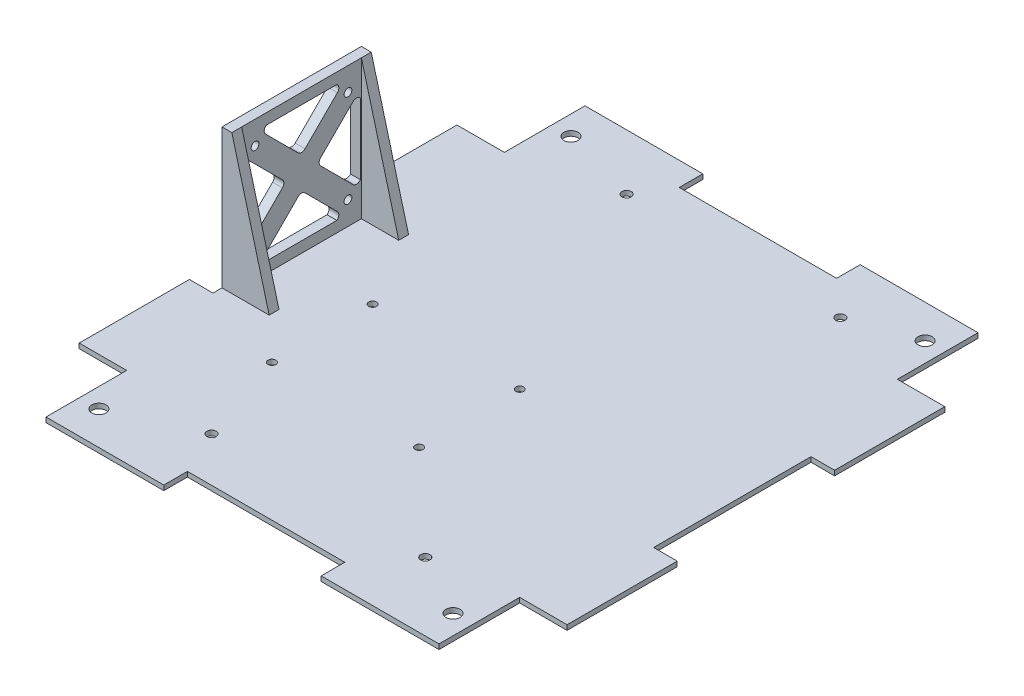
SolidWorks part; units mm, degrees
ref_plane "Front Plane" through (0, 0, 0) normal (0, 0, 1) x (1, 0, 0)
ref_plane "Top Plane" through (0, 0, 0) normal (0, 1, 0) x (1, 0, 0)
ref_plane "Right Plane" through (0, 0, 0) normal (1, 0, 0) x (0, 0, -1)
sketch "Sketch1" plane through (0, 0, 0) normal (0, 1, 0) x (1, 0, 0)
  line L0 (-25.4, 86.995) -> (-63.4314, 86.995)
  line L1 (-88.9, -101.6) -> (88.9, -101.6) construction
  line L2 (101.6, -88.9) -> (101.6, 88.9) construction
  line L3 (88.9, 101.6) -> (-88.9, 101.6) construction
  line L4 (-78.74, -60.96) -> (-63.4314, -60.96)
  line L5 (-63.4314, -60.96) -> (-63.4314, -86.995)
  line L6 (-63.4314, -86.995) -> (-25.4, -86.995)
  line L7 (63.4314, -86.995) -> (63.4314, -60.96)
  line L8 (63.4314, -60.96) -> (78.74, -60.96)
  line L9 (78.74, -60.96) -> (78.74, -25.4)
  line L10 (78.74, 60.96) -> (63.4314, 60.96)
  line L11 (63.4314, 60.96) -> (63.4314, 86.995)
  line L12 (63.4314, 86.995) -> (25.4, 86.995)
  line L13 (-63.4314, 86.995) -> (-63.4314, 60.96)
  line L14 (-63.4314, 60.96) -> (-78.74, 60.96)
  line L15 (-78.74, 60.96) -> (-78.74, 25.4)
  line L16 (-78.74, -25.4) -> (-78.74, -60.96)
  line L17 (-78.74, -25.4) -> (-71.12, -25.4)
  line L19 (-78.74, 25.4) -> (-71.12, 25.4)
  line L20 (-71.12, -25.4) -> (-71.12, 25.4)
  line L22 (-25.4, 86.995) -> (-25.4, 79.375)
  line L23 (-25.4, 79.375) -> (25.4, 79.375)
  line L24 (25.4, 86.995) -> (25.4, 79.375)
  line L25 (78.74, 25.4) -> (71.12, 25.4)
  line L27 (78.74, -25.4) -> (71.12, -25.4)
  line L28 (71.12, 25.4) -> (71.12, -25.4)
  line L30 (25.4, -86.995) -> (25.4, -79.375)
  line L31 (25.4, -79.375) -> (-25.4, -79.375)
  line L32 (-25.4, -86.995) -> (-25.4, -79.375)
  line L33 (78.74, 25.4) -> (78.74, 60.96)
  line L34 (25.4, -86.995) -> (63.4314, -86.995)
  line L35 (-101.6, 88.9) -> (-101.6, -88.9) construction
  arc A0 (88.9, -101.6) -> (101.6, -88.9) centre (88.9, -88.9) ccw construction
  arc A1 (-101.6, -88.9) -> (-88.9, -101.6) centre (-88.9, -88.9) ccw construction
  arc A2 (101.6, 88.9) -> (88.9, 101.6) centre (88.9, 88.9) ccw construction
  arc A3 (-101.6, 88.9) -> (-88.9, 101.6) centre (-88.9, 88.9) cw construction
  circle A4 centre (-57.15, 76.2) radius 2.286
  circle A5 centre (57.15, 76.2) radius 2.286
  circle A6 centre (57.15, -76.2) radius 2.286
  circle A7 centre (-57.15, -76.2) radius 2.286
  point P3 (0, 101.6)
  point P5 (101.6, 0)
  point P13 (101.6, 101.6)
  point P16 (-101.6, 101.6)
  point P38 (-71.12, 0)
  point P55 (0, -79.375)
  point P56 (0, 79.375)
  point P57 (71.12, 0)
  dimension "D2" = 12.7
  dimension "D11" = 4.572
  dimension "D8" = 44.45
  dimension "D1" = 203.2
  dimension "D3" = 203.2
  dimension "D4" = 22.86
  dimension "D5" = 15.3086
  dimension "D6" = 35.56
  dimension "D7" = 173.99
  dimension "D12" = 50.8
  dimension "D13" = 25.4
  dimension "D14" = 44.45
  dimension "D15" = 25.4
  dimension "D18" = 7.62
extrude "Main Body" add sketch "Sketch1" along normal blind 1.5875
sketch "Sketch8" plane through (0, 1.5875, 0) normal (0, 1, 0) x (1, 0, 0)
  line L1 (-71.12, 22.5) -> (-67.945, 22.5)
  line L2 (-71.12, 22.5) -> (-71.12, -22.5)
  line L3 (-71.12, -22.5) -> (-67.945, -22.5)
  line L4 (-67.945, 22.5) -> (-67.945, -22.5)
  line L5 (-71.12, 22.5) -> (-67.945, -22.5) construction
  line L6 (-71.12, -22.5) -> (-67.945, 22.5) construction
  line L34 (71.12, -25.4) -> (71.12, 25.4)
  line L35 (71.12, 25.4) -> (78.74, 25.4)
  line L36 (78.74, 25.4) -> (78.74, 60.96)
  line L37 (78.74, 60.96) -> (63.4314, 60.96)
  line L38 (63.4314, 60.96) -> (63.4314, 86.995)
  line L39 (63.4314, 86.995) -> (25.4, 86.995)
  line L40 (25.4, 86.995) -> (25.4, 79.375)
  line L41 (25.4, 79.375) -> (-25.4, 79.375)
  line L42 (-25.4, 79.375) -> (-25.4, 86.995)
  line L43 (-25.4, 86.995) -> (-63.4314, 86.995)
  line L44 (-63.4314, 86.995) -> (-63.4314, 60.96)
  line L45 (-63.4314, 60.96) -> (-78.74, 60.96)
  line L46 (-78.74, 60.96) -> (-78.74, 25.4)
  line L47 (-78.74, 25.4) -> (-71.12, 25.4)
  line L48 (-71.12, 25.4) -> (-71.12, -25.4)
  line L49 (-71.12, -25.4) -> (-78.74, -25.4)
  line L50 (-78.74, -25.4) -> (-78.74, -60.96)
  line L51 (-78.74, -60.96) -> (-63.4314, -60.96)
  line L52 (-63.4314, -60.96) -> (-63.4314, -86.995)
  line L53 (-63.4314, -86.995) -> (-25.4, -86.995)
  line L54 (-25.4, -86.995) -> (-25.4, -79.375)
  line L55 (-25.4, -79.375) -> (25.4, -79.375)
  line L56 (25.4, -79.375) -> (25.4, -86.995)
  line L57 (25.4, -86.995) -> (63.4314, -86.995)
  line L58 (63.4314, -86.995) -> (63.4314, -60.96)
  line L59 (63.4314, -60.96) -> (78.74, -60.96)
  line L60 (78.74, -60.96) -> (78.74, -25.4)
  line L61 (78.74, -25.4) -> (71.12, -25.4)
  line L66 (71.12, -25.4) -> (71.12, 25.4)
  line L67 (71.12, 25.4) -> (78.74, 25.4)
  line L68 (78.74, 25.4) -> (78.74, 60.96)
  line L69 (78.74, 60.96) -> (63.4314, 60.96)
  line L70 (63.4314, 60.96) -> (63.4314, 86.995)
  line L71 (63.4314, 86.995) -> (25.4, 86.995)
  line L72 (25.4, 86.995) -> (25.4, 79.375)
  line L73 (25.4, 79.375) -> (-25.4, 79.375)
  line L74 (-25.4, 79.375) -> (-25.4, 86.995)
  line L75 (-25.4, 86.995) -> (-63.4314, 86.995)
  line L76 (-63.4314, 86.995) -> (-63.4314, 60.96)
  line L77 (-63.4314, 60.96) -> (-78.74, 60.96)
  line L78 (-78.74, 60.96) -> (-78.74, 25.4)
  line L79 (-78.74, 25.4) -> (-71.12, 25.4)
  line L80 (-71.12, 25.4) -> (-71.12, -25.4)
  line L81 (-71.12, -25.4) -> (-78.74, -25.4)
  line L82 (-78.74, -25.4) -> (-78.74, -60.96)
  line L83 (-78.74, -60.96) -> (-63.4314, -60.96)
  line L84 (-63.4314, -60.96) -> (-63.4314, -86.995)
  line L85 (-63.4314, -86.995) -> (-25.4, -86.995)
  line L86 (-25.4, -86.995) -> (-25.4, -79.375)
  line L87 (-25.4, -79.375) -> (25.4, -79.375)
  line L88 (25.4, -79.375) -> (25.4, -86.995)
  line L89 (25.4, -86.995) -> (63.4314, -86.995)
  line L90 (63.4314, -86.995) -> (63.4314, -60.96)
  line L91 (63.4314, -60.96) -> (78.74, -60.96)
  line L92 (78.74, -60.96) -> (78.74, -25.4)
  line L93 (78.74, -25.4) -> (71.12, -25.4)
  point P2 (-71.12, 0)
  point P4 (-69.5325, 0)
  line M61 (-71.12, 25.4) -> (-71.12, -25.4)
  dimension "D2" = 3.175
  dimension "D3" = 45
  dimension "D1" = 0
extrude "Boss-Extrude4" add sketch "Sketch8" along normal blind 45 contours L4 L1 L3 M61
sketch "Sketch9" plane through (-71.12, 0, 0) normal (-1, 0, 0) x (0, 0, 1)
  line L2 (-19, 5.0875) -> (19, 5.0875)
  line L3 (-19, 5.0875) -> (-19, 43.0875)
  line L4 (-19, 43.0875) -> (19, 43.0875)
  line L5 (19, 5.0875) -> (19, 43.0875)
  line L8 (-25.4, 0) -> (25.4, 0)
  line L9 (25.4, 0) -> (25.4, 1.5875)
  line L10 (25.4, 1.5875) -> (22.5, 1.5875)
  line L11 (22.5, 1.5875) -> (22.5, 46.5875)
  line L12 (22.5, 46.5875) -> (-22.5, 46.5875)
  line L13 (-22.5, 46.5875) -> (-22.5, 1.5875)
  line L14 (-22.5, 1.5875) -> (-25.4, 1.5875)
  line L15 (-25.4, 1.5875) -> (-25.4, 0)
  line L16 (-25.4, 0) -> (25.4, 0)
  line L17 (25.4, 0) -> (25.4, 1.5875)
  line L18 (25.4, 1.5875) -> (22.5, 1.5875)
  line L19 (22.5, 1.5875) -> (22.5, 46.5875)
  line L20 (22.5, 46.5875) -> (-22.5, 46.5875)
  line L21 (-22.5, 46.5875) -> (-22.5, 1.5875)
  line L22 (-22.5, 1.5875) -> (-25.4, 1.5875)
  line L23 (-25.4, 1.5875) -> (-25.4, 0)
  line L24 (-1.1225, 30.2475) -> (-11.5775, 40.7025)
  line L25 (1.1225, 30.2475) -> (11.5775, 40.7025)
  line L26 (10.4549, 43.4125) -> (-10.4549, 43.4125)
  line L27 (19.325, 13.6326) -> (19.325, 34.5424)
  line L28 (6.16, 25.21) -> (16.615, 35.665)
  line L29 (6.16, 22.965) -> (16.615, 12.51)
  line L30 (-10.4549, 4.7625) -> (10.4549, 4.7625)
  line L31 (1.1225, 17.9275) -> (11.5775, 7.4725)
  line L32 (-1.1225, 17.9275) -> (-11.5775, 7.4725)
  line L33 (-19.325, 34.5424) -> (-19.325, 13.6326)
  line L34 (-6.16, 22.965) -> (-16.615, 12.51)
  line L35 (-6.16, 25.21) -> (-16.615, 35.665)
  circle A0 centre (-15, 39.0875) radius 1.25
  circle A1 centre (15, 39.0875) radius 1.25
  circle A2 centre (-15, 9.0875) radius 1.25
  circle A3 centre (15, 9.0875) radius 1.25
  arc A4 (10.4549, 43.4125) -> (11.5775, 40.7025) centre (10.4549, 41.825) cw
  arc A5 (1.1225, 30.2475) -> (-1.1225, 30.2475) centre (0, 31.3701) cw
  arc A6 (-11.5775, 40.7025) -> (-10.4549, 43.4125) centre (-10.4549, 41.825) cw
  arc A7 (16.615, 35.665) -> (19.325, 34.5424) centre (17.7375, 34.5424) cw
  arc A8 (19.325, 13.6326) -> (16.615, 12.51) centre (17.7375, 13.6326) cw
  arc A9 (6.16, 22.965) -> (6.16, 25.21) centre (7.2826, 24.0875) cw
  arc A10 (11.5775, 7.4725) -> (10.4549, 4.7625) centre (10.4549, 6.35) cw
  arc A11 (-10.4549, 4.7625) -> (-11.5775, 7.4725) centre (-10.4549, 6.35) cw
  arc A12 (-1.1225, 17.9275) -> (1.1225, 17.9275) centre (0, 16.8049) cw
  arc A13 (-16.615, 12.51) -> (-19.325, 13.6326) centre (-17.7375, 13.6326) cw
  arc A14 (-19.325, 34.5424) -> (-16.615, 35.665) centre (-17.7375, 34.5424) cw
  arc A15 (-6.16, 25.21) -> (-6.16, 22.965) centre (-7.2826, 24.0875) cw
  point P24 (0, 29.125)
  point P30 (14.2875, 43.4125)
  point P33 (0, 29.125)
  point P36 (-14.2875, 43.4125)
  point P67 (0, 24.0875)
  dimension "D6" = 2.5
  dimension "D15" = 1.5875
  dimension "D18" = 22.5
  dimension "D2" = 19
  dimension "D3" = 19
  dimension "D4" = 38
  dimension "D5" = 38
  dimension "D7" = 4
  dimension "D8" = 4
  dimension "D9" = 4
  dimension "D10" = 4
  dimension "D11" = 45
  dimension "D12" = 45
  dimension "D13" = 28.575
  dimension "D14" = 3.175
  dimension "D17" = 5.0375
  dimension "D19" = 22.5
  dimension "D1" = 0
  dimension "D16" = 4
sketch "Sketch10" plane through (0, 0, 22.5) normal (0, 0, 1) x (1, 0, 0)
  line L3 (-67.945, 46.5875) -> (-67.945, 1.5875) construction
  line L4 (-67.945, 46.5875) -> (-67.945, 1.5875)
  line L5 (-67.945, 46.5875) -> (-55.8873, 1.5875)
  line L6 (-55.8873, 1.5875) -> (-67.945, 1.5875)
  dimension "D1" = 15
extrude "Boss-Extrude5" add sketch "Sketch10" against normal blind 3.175 contours L6 L4 L5
mirror "Mirror3" about plane through (0, 0, 0) normal (0, 0, 1) of "Boss-Extrude5"
extrude "Cut-Extrude2" cut sketch "Sketch9" against normal up to next contours A15 L35 A14 L3 A13 L34 | A9 L29 A8 L5 A7 L28 | A12 L32 A11 L2 A10 L31 | A6 L24 A5 L25 A4 L4 | A1 | A0 | A2 | A3
sketch "Sketch12" plane through (0, 0, 0) normal (0, -1, 0) x (1, 0, 0)
  line L1 (-45, -80) -> (45, -80)
  line L2 (-45, -80) -> (-45, 80)
  line L3 (-45, 80) -> (45, 80)
  line L4 (45, -80) -> (45, 80)
  line L5 (-45, -80) -> (45, 80) construction
  line L6 (-45, 80) -> (45, -80) construction
  line L7 (-39.779, -55.547) -> (-27.7357, -55.547)
  line L8 (-39.779, -55.547) -> (-39.779, -29.6043)
  line L9 (-39.779, -29.6043) -> (-27.7357, -29.6043)
  line L10 (-27.7357, -55.547) -> (-27.7357, -29.6043)
  line L11 (-39.779, -55.547) -> (-27.7357, -29.6043) construction
  line L12 (-39.779, -29.6043) -> (-27.7357, -55.547) construction
  line L13 (-29.9932, -76.7863) -> (-5.1713, -76.7863)
  line L14 (-29.9932, -76.7863) -> (-29.9932, -67.2902)
  line L15 (-29.9932, -67.2902) -> (-5.1713, -67.2902)
  line L16 (-5.1713, -76.7863) -> (-5.1713, -67.2902)
  line L17 (-29.9932, -76.7863) -> (-5.1713, -67.2902) construction
  line L18 (-29.9932, -67.2902) -> (-5.1713, -76.7863) construction
  line L28 (-78.74, 60.96) -> (-78.74, 25.4)
  line L29 (-78.74, 25.4) -> (-71.12, 25.4)
  line L30 (-71.12, 25.4) -> (-71.12, -25.4)
  line L31 (-71.12, -25.4) -> (-78.74, -25.4)
  line L32 (-78.74, -25.4) -> (-78.74, -60.96)
  line L33 (-78.74, -60.96) -> (-63.4314, -60.96)
  line L34 (-63.4314, -60.96) -> (-63.4314, -86.995)
  line L35 (-63.4314, -86.995) -> (-25.4, -86.995)
  line L36 (-25.4, -86.995) -> (-25.4, -79.375)
  line L37 (-25.4, -79.375) -> (25.4, -79.375)
  line L38 (25.4, -79.375) -> (25.4, -86.995)
  line L39 (25.4, -86.995) -> (63.4314, -86.995)
  line L40 (63.4314, -86.995) -> (63.4314, -60.96)
  line L41 (63.4314, -60.96) -> (78.74, -60.96)
  line L42 (78.74, -60.96) -> (78.74, -25.4)
  line L43 (78.74, -25.4) -> (71.12, -25.4)
  line L44 (71.12, -25.4) -> (71.12, 25.4)
  line L45 (71.12, 25.4) -> (78.74, 25.4)
  line L46 (78.74, 25.4) -> (78.74, 60.96)
  line L47 (78.74, 60.96) -> (63.4314, 60.96)
  line L48 (63.4314, 60.96) -> (63.4314, 86.995)
  line L49 (63.4314, 86.995) -> (25.4, 86.995)
  line L50 (25.4, 86.995) -> (25.4, 79.375)
  line L51 (25.4, 79.375) -> (-25.4, 79.375)
  line L52 (-25.4, 79.375) -> (-25.4, 86.995)
  line L53 (-25.4, 86.995) -> (-63.4314, 86.995)
  line L54 (-63.4314, 86.995) -> (-63.4314, 60.96)
  line L55 (-63.4314, 60.96) -> (-78.74, 60.96)
  line L56 (-78.74, 60.96) -> (-78.74, 25.4)
  line L57 (-78.74, 25.4) -> (-71.12, 25.4)
  line L58 (-71.12, 25.4) -> (-71.12, -25.4)
  line L59 (-71.12, -25.4) -> (-78.74, -25.4)
  line L60 (-78.74, -25.4) -> (-78.74, -60.96)
  line L61 (-78.74, -60.96) -> (-63.4314, -60.96)
  line L62 (-63.4314, -60.96) -> (-63.4314, -86.995)
  line L63 (-63.4314, -86.995) -> (-25.4, -86.995)
  line L64 (-25.4, -86.995) -> (-25.4, -79.375)
  line L65 (-25.4, -79.375) -> (25.4, -79.375)
  line L66 (25.4, -79.375) -> (25.4, -86.995)
  line L67 (25.4, -86.995) -> (63.4314, -86.995)
  line L68 (63.4314, -86.995) -> (63.4314, -60.96)
  line L69 (63.4314, -60.96) -> (78.74, -60.96)
  line L70 (78.74, -60.96) -> (78.74, -25.4)
  line L71 (78.74, -25.4) -> (71.12, -25.4)
  line L72 (71.12, -25.4) -> (71.12, 25.4)
  line L73 (71.12, 25.4) -> (78.74, 25.4)
  line L74 (78.74, 25.4) -> (78.74, 60.96)
  line L75 (78.74, 60.96) -> (63.4314, 60.96)
  line L76 (63.4314, 60.96) -> (63.4314, 86.995)
  line L77 (63.4314, 86.995) -> (25.4, 86.995)
  line L78 (25.4, 86.995) -> (25.4, 79.375)
  line L79 (25.4, 79.375) -> (-25.4, 79.375)
  line L80 (-25.4, 79.375) -> (-25.4, 86.995)
  line L81 (-25.4, 86.995) -> (-63.4314, 86.995)
  line L82 (-63.4314, 86.995) -> (-63.4314, 60.96)
  line L83 (-63.4314, 60.96) -> (-78.74, 60.96)
  circle A0 centre (-32, -69) radius 1.5
  circle A1 centre (37, -69) radius 1.5
  circle A2 centre (37, 65) radius 1.5
  circle A3 centre (-32, 65) radius 1.5
  circle A4 centre (-42.25, 2.75) radius 1.25
  circle A5 centre (-42.25, 35.25) radius 1.25
  circle A6 centre (5.25, 2.75) radius 1.25
  circle A7 centre (5.25, 35.25) radius 1.25
  point P2 (0, 0)
  point P12 (-33.7573, -42.5756)
  point P22 (-17.5822, -72.0382)
  dimension "D4" = 3
  dimension "D9" = 2.5
  dimension "D2" = 90
  dimension "D3" = 160
  dimension "D5" = 11
  dimension "D6" = 145
  dimension "D7" = 8
  dimension "D8" = 77
  dimension "D10" = 32.5
  dimension "D11" = 47.5
  dimension "D12" = 2.75
  dimension "D13" = 44.75
  dimension "D1" = 0
extrude "Cut-Extrude3" cut sketch "Sketch12" against normal up to next contours A3 | A2 | A1 | A0 | A4 | A5 | A7 | A6
